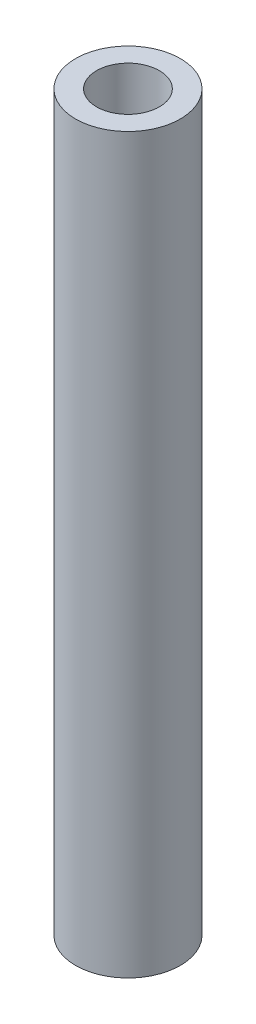
SolidWorks part; units mm, degrees
ref_plane "前视基准面" through (0, 0, 0) normal (0, 0, 1) x (1, 0, 0)
ref_plane "上视基准面" through (0, 0, 0) normal (0, 1, 0) x (1, 0, 0)
ref_plane "右视基准面" through (0, 0, 0) normal (1, 0, 0) x (0, 0, -1)
sketch "草图1" plane through (0, 0, 0) normal (0, 1, 0) x (1, 0, 0)
  circle A0 centre (0, 0) radius 1.5
  circle A1 centre (0, 0) radius 2.5
  dimension "D1" = 5
  dimension "D2" = 3
extrude "凸台-拉伸1" add sketch "草图1" along normal blind 35
